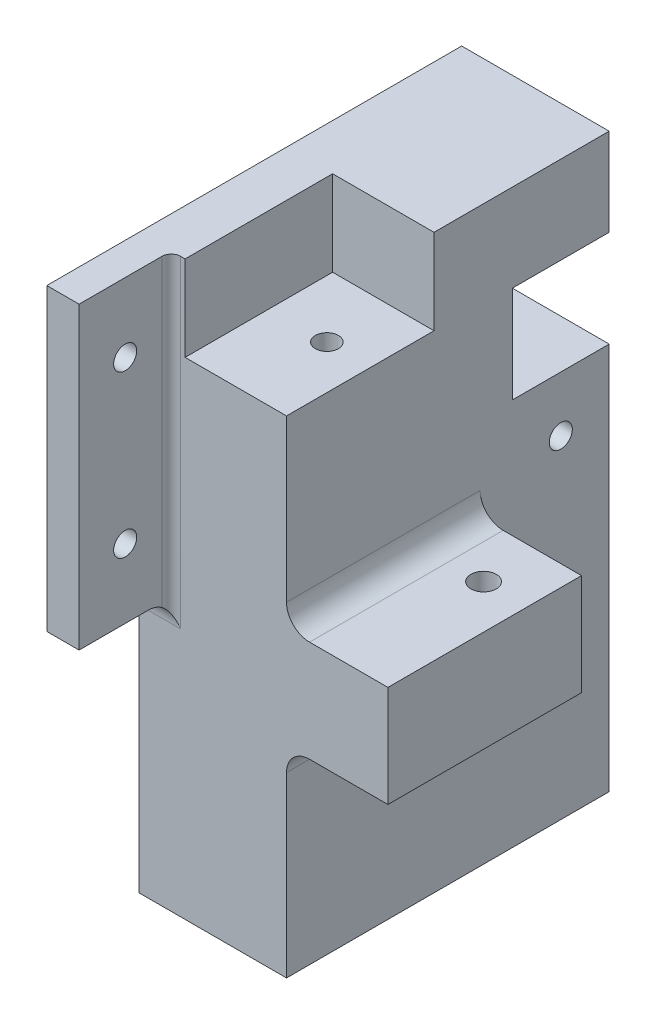
SolidWorks part; units mm, degrees
ref_plane "Front" through (0, 0, 0) normal (0, 0, 1) x (1, 0, 0)
ref_plane "Top" through (0, 0, 0) normal (0, 1, 0) x (1, 0, 0)
ref_plane "Right" through (0, 0, 0) normal (1, 0, 0) x (0, 0, -1)
sketch "Sketch1" plane through (0, 0, 0) normal (0, 1, 0) x (1, 0, 0)
  line L1 (-16, 35) -> (16, 35)
  line L2 (-16, 35) -> (-16, -35)
  line L3 (-16, -35) -> (16, -35)
  line L4 (16, 35) -> (16, -35)
  line L5 (-16, 35) -> (16, -35) construction
  line L6 (-16, -35) -> (16, 35) construction
  point P0 (0, 0)
  dimension "D1" = 70
  dimension "D2" = 32
extrude "Boss-Extrude1" add sketch "Sketch1" against normal blind 84.1 and the other way blind 40
sketch "Sketch2" plane through (0, 0, 0) normal (1, 0, 0) x (0, 0, -1)
  line L0 (35, 40) -> (35, -84.1) construction
  line L1 (35, 21) -> (14, 21)
  line L2 (35, 21) -> (35, 0)
  line L3 (35, 0) -> (14, 0)
  line L4 (14, 21) -> (14, 0)
  line L5 (35, 21) -> (14, 0) construction
  line L6 (35, 0) -> (14, 21) construction
  point P0 (24.5, 10.5)
  dimension "D1" = 21
extrude "Cut-Extrude1" cut sketch "Sketch2" against normal through all both and the other way through all
sketch "Sketch3" plane through (0, 40, 0) normal (0, 1, 0) x (1, 0, 0)
  line L0 (-6, -35) -> (-6, -3)
  line L1 (-16, -35) -> (16, -35) construction
  line L2 (-6, -3) -> (16, -3)
  line L3 (16, -35) -> (16, 35) construction
  line L4 (-6, -35) -> (16, -35)
  line L5 (16, -35) -> (16, -3)
  dimension "D1" = 32
  dimension "D2" = 22
extrude "Cut-Extrude2" cut sketch "Sketch3" against normal up to surface (18.5 mm away)
sketch "Sketch4" plane through (16, 0, 0) normal (1, 0, 0) x (0, 0, -1)
  line L0 (-35, -18.5) -> (7, -18.5)
  line L1 (-35, 21.5) -> (-35, -84.1) construction
  line L2 (7, -18.5) -> (7, -40.5)
  line L3 (7, -40.5) -> (-35, -40.5)
  line L4 (-35, -40.5) -> (-35, -18.5)
  line L7 (-35, 21.5) -> (-3, 21.5) construction
  point P6 (10, -34.6742)
  dimension "D1" = 42
  dimension "D2" = 40
  dimension "D3" = 22
extrude "Boss-Extrude2" add sketch "Sketch4" along normal blind 22
sketch "Sketch5" plane through (0, -18.5, 0) normal (0, 1, 0) x (1, 0, 0)
  line L0 (38, 7) -> (16, 7) construction
  line L1 (16, 7) -> (16, -35) construction
  circle A0 centre (28.5, -4.75) radius 2.75
  point P4 (0, 0)
  point P5 (0, 0)
  dimension "D2" = 5.5
  dimension "D1" = 11.75
  dimension "D3" = 12.5
extrude "Cut-Extrude3" cut sketch "Sketch5" against normal through all
sketch "Sketch6" plane through (0, 0, 35) normal (0, 0, 1) x (1, 0, 0)
  line L0 (-16, 40) -> (-9, 40)
  line L1 (-16, 40) -> (-6, 40) construction
  line L2 (-9, 40) -> (-9, -25)
  line L3 (-9, -25) -> (-16, -25)
  line L4 (-16, 40) -> (-16, -84.1) construction
  line L5 (-16, -25) -> (-16, 40)
  dimension "D1" = 7
  dimension "D2" = 65
extrude "Boss-Extrude3" add sketch "Sketch6" along normal blind 20
sketch "Sketch7" plane through (0, 0, 0) normal (-1, 0, 0) x (0, 0, 1)
  line L0 (-14, 0) -> (-35, 0) construction
  circle A0 centre (-24.5, -12) radius 2.5
  point P4 (0, 0)
  point P5 (-24.5, 0)
  dimension "D1" = 5
  dimension "D2" = 12
extrude "Cut-Extrude4" cut sketch "Sketch7" against normal through all both and the other way through all
sketch "Sketch8" plane through (-9, 0, 0) normal (1, 0, 0) x (0, 0, -1)
  line L0 (-55, -25) -> (-35, -25) construction
  line L1 (-55, 40) -> (-35, 40) construction
  circle A0 centre (-45, 25) radius 2.5
  circle A1 centre (-45, -10) radius 2.5
  point P8 (0, 0)
  point P9 (-47.5333, -10)
  point P10 (0, 0)
  point P11 (-45, 40)
  dimension "D1" = 5
  dimension "D2" = 15
  dimension "D3" = 15
extrude "Cut-Extrude5" cut sketch "Sketch8" against normal through all
fillet "Fillet1" radius 2 1 edges at (-9, 7.5, 35)
fillet "Fillet2" radius 5 3 edges at (-11.5, -25, 35) (16, -40.5, 14) (16, -18.5, 14)
sketch "Sketch9" plane through (0, 21.5, 0) normal (0, 1, 0) x (1, 0, 0)
  line L0 (16, -3) -> (-6, -3) construction
  line L1 (-6, -3) -> (-6, -35) construction
  circle A0 centre (6.5, -16.75) radius 2.5
  point P4 (0, 0)
  dimension "D2" = 5
  dimension "D1" = 13.75
  dimension "D3" = 12.5
extrude "Cut-Extrude6" cut sketch "Sketch9" against normal blind 47.45
